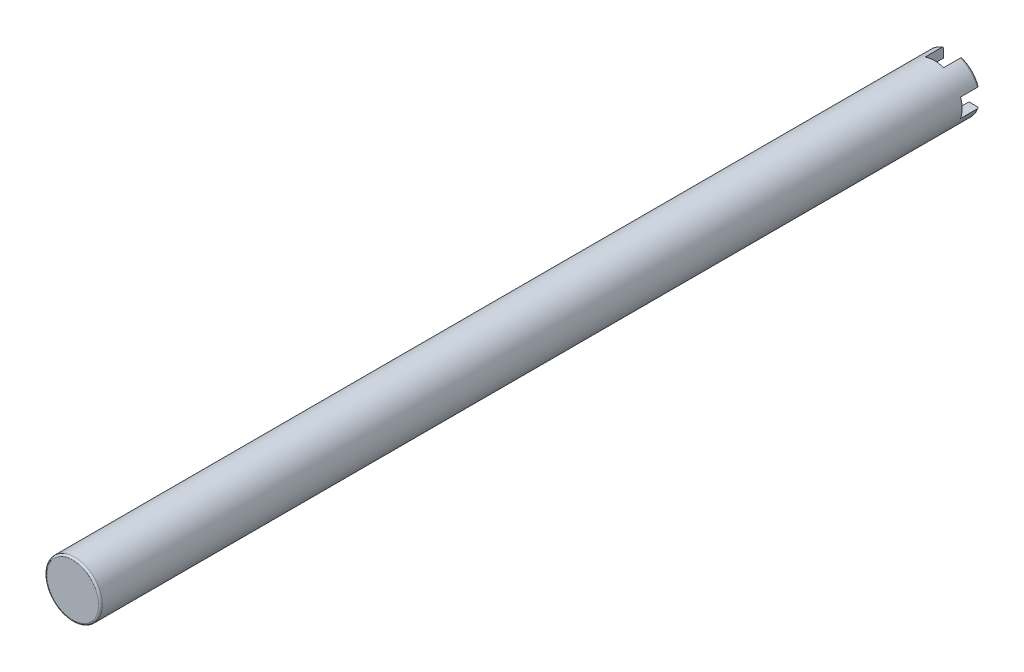
SolidWorks part; units mm, degrees
ref_plane "Front Plane" through (0, 0, 0) normal (0, 0, 1) x (1, 0, 0)
ref_plane "Top Plane" through (0, 0, 0) normal (0, 1, 0) x (1, 0, 0)
ref_plane "Right Plane" through (0, 0, 0) normal (1, 0, 0) x (0, 0, -1)
sketch "Sketch1" plane through (0, 0, 0) normal (0, 0, 1) x (1, 0, 0)
  circle A0 centre (0, 0) radius 38.1
  dimension "D1" = 76.2
extrude "Boss-Extrude1" add sketch "Sketch1" along normal blind 1206.5
fillet "Fillet1" radius 2.54 1 edges at (38.1, 0, 1206.5)
fillet "Fillet2" radius 2.54 1 edges at (38.1, 0, 0)
sketch "Sketch3" plane through (0, 0, 0) normal (0, 0, -1) x (-1, 0, 0)
  line L5 (12.7, 12.7) -> (64.1368, 12.7)
  line L7 (12.7, -12.7) -> (64.1368, -12.7)
  line L8 (64.1368, 12.7) -> (64.1368, -12.7)
  line L9 (-12.7, 12.7) -> (-64.7656, 12.7)
  line L11 (-12.7, -12.7) -> (-64.7656, -12.7)
  line L12 (-64.7656, 12.7) -> (-64.7656, -12.7)
  line L14 (-12.7, -12.7) -> (-12.7, -42.915)
  line L15 (-12.7, -42.915) -> (12.7, -42.915)
  line L16 (12.7, -12.7) -> (12.7, -42.915)
  line L18 (-12.7, 12.7) -> (-12.7, 40.7143)
  line L19 (-12.7, 40.7143) -> (12.7, 40.7143)
  line L20 (12.7, 12.7) -> (12.7, 40.7143)
  dimension "D1" = 25.4
  dimension "D2" = 25.4
extrude "Cut-Extrude2" cut sketch "Sketch3" against normal blind 25.4 contours L9 L12 L11 L14 L15 L16 L7 L8 L5 L20 L19 L18
sketch "Sketch2" plane through (0, 0, 0) normal (0, 0, -1) x (-1, 0, 0)
  circle A0 centre (0, 0) radius 25.4
  dimension "D1" = 50.8
extrude "Cut-Extrude1" cut sketch "Sketch2" against normal blind 609.6
